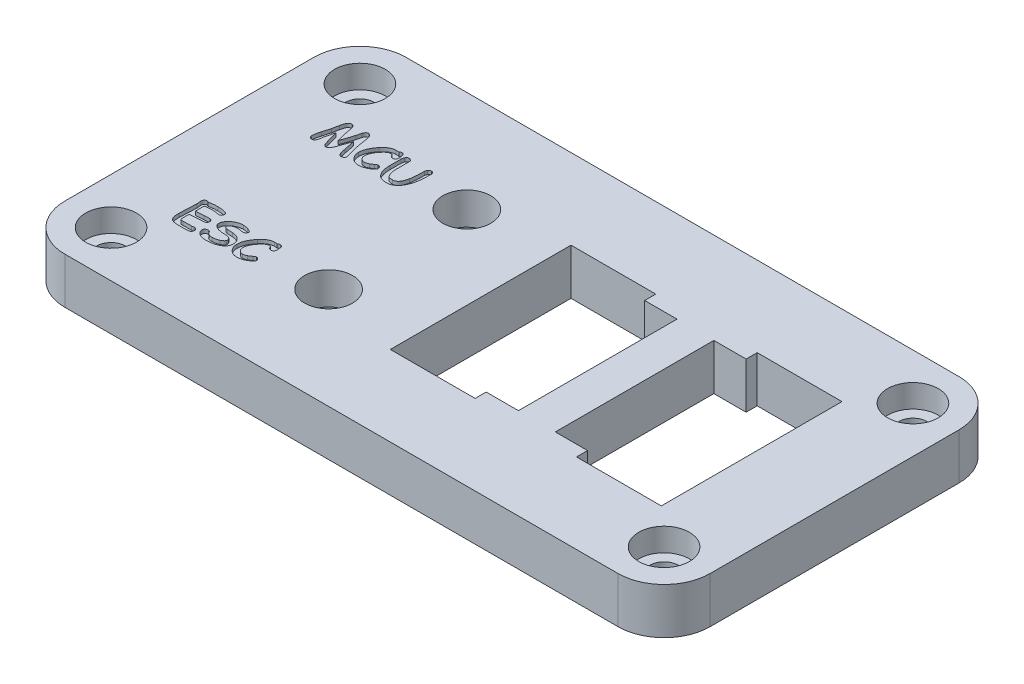
SolidWorks part; units mm, degrees
ref_plane "Front Plane" through (0, 0, 0) normal (0, 0, 1) x (1, 0, 0)
ref_plane "Top Plane" through (0, 0, 0) normal (0, 1, 0) x (1, 0, 0)
ref_plane "Right Plane" through (0, 0, 0) normal (1, 0, 0) x (0, 0, -1)
sketch "Sketch1" plane through (0, 0, 0) normal (0, 1, 0) x (1, 0, 0)
  line L0 (-1000, 0) -> (49000, 0) construction
  line L1 (-35, -18.5) -> (35, -18.5)
  line L2 (-35, -18.5) -> (-35, 18.5)
  line L3 (-35, 18.5) -> (35, 18.5)
  line L4 (35, -18.5) -> (35, 18.5)
  line L5 (-35, -18.5) -> (35, 18.5) construction
  line L6 (-35, 18.5) -> (35, -18.5) construction
  line L7 (-1002.5399, 13.5) -> (48997.4601, 13.5) construction
  line L8 (-1000.0562, -13.5) -> (48999.9438, -13.5) construction
  line L9 (-12.4, -1000) -> (-12.4, 49000) construction
  line L10 (26, -8.6) -> (13.3, -8.6)
  line L11 (26, -8.6) -> (26, 8.6)
  line L12 (26, 8.6) -> (13.3, 8.6)
  line L13 (13.3, -8.6) -> (13.3, 8.6)
  line L14 (26, -8.6) -> (13.3, 8.6) construction
  line L15 (26, 8.6) -> (13.3, -8.6) construction
  line L16 (26, 8.6) -> (16.8, 8.6)
  line L17 (26, 8.6) -> (26, 9.8)
  line L18 (26, 9.8) -> (16.8, 9.8)
  line L19 (16.8, 8.6) -> (16.8, 9.8)
  line L20 (26, -8.6) -> (16.8, -8.6)
  line L21 (26, -8.6) -> (26, -9.8)
  line L22 (26, -9.8) -> (16.8, -9.8)
  line L23 (16.8, -8.6) -> (16.8, -9.8)
  line L24 (-3.4, -8.6) -> (9.3, -8.6)
  line L25 (-3.4, -8.6) -> (-3.4, 8.6)
  line L26 (-3.4, 8.6) -> (9.3, 8.6)
  line L27 (9.3, -8.6) -> (9.3, 8.6)
  line L28 (-3.4, -8.6) -> (9.3, 8.6) construction
  line L29 (-3.4, 8.6) -> (9.3, -8.6) construction
  line L38 (-30, -986.4854) -> (-30, 49013.5146) construction
  line L39 (30, -986.4123) -> (30, 49013.5877) construction
  line L41 (-3.4, 8.6) -> (5.8, 8.6)
  line L42 (-3.4, 8.6) -> (-3.4, 9.8)
  line L43 (-3.4, 9.8) -> (5.8, 9.8)
  line L44 (5.8, 8.6) -> (5.8, 9.8)
  line L45 (-3.4, -8.6) -> (5.8, -8.6)
  line L46 (-3.4, -8.6) -> (-3.4, -9.8)
  line L47 (-3.4, -9.8) -> (5.8, -9.8)
  line L48 (5.8, -8.6) -> (5.8, -9.8)
  circle A0 centre (-12.4, 7.5) radius 2.6
  circle A1 centre (-12.4, -7.5) radius 2.6
  circle A2 centre (30, 13.5) radius 1.55
  circle A3 centre (30, -13.5) radius 1.55
  circle A4 centre (-30, -13.5) radius 1.55
  circle A5 centre (-30, 13.5) radius 1.55
  point P0 (0, 0)
  point P11 (19.65, 0)
  point P23 (2.95, 0)
  dimension "D20" = 5.2
  dimension "D21" = 5.2
  dimension "D26" = 3.1
  dimension "D28" = 3.1
  dimension "D30" = 3.1
  dimension "D32" = 3.1
  dimension "D1" = 37
  dimension "D2" = 70
  dimension "D3" = 5
  dimension "D4" = 5
  dimension "D5" = 17.2
  dimension "D6" = 12.7
  dimension "D7" = 9
  dimension "D8" = 1.2
  dimension "D9" = 1.2
  dimension "D10" = 9.2
  dimension "D11" = 9.2
  dimension "D12" = 12.7
  dimension "D13" = 17.2
  dimension "D14" = 4
  dimension "D15" = 1.2
  dimension "D16" = 1.2
  dimension "D17" = 9.2
  dimension "D18" = 9.2
  dimension "D19" = 9
  dimension "D22" = 7.5
  dimension "D23" = 7.5
  dimension "D24" = 5
  dimension "D25" = 5
  dimension "D27" = 0
  dimension "D29" = 0
  dimension "D31" = 0
  dimension "D33" = 0
extrude "Boss-Extrude1" add sketch "Sketch1" along normal blind 5 contours L1 L4 L3 L2 A5 A4 A3 A2 A1 A0 L23 L10 L13 L12 L19 L18 L17 L11 L21 L22 L24 L48 L47 L46 L25 L42 L43 L44 L26 L27
sketch "Sketch2" plane through (0, 5, 0) normal (0, 1, 0) x (1, 0, 0)
  circle A0 centre (-30, 13.5) radius 2.75
  circle A1 centre (30, 13.5) radius 2.75
  circle A2 centre (30, -13.5) radius 2.75
  circle A3 centre (-30, -13.5) radius 2.75
  dimension "D1" = 5.5
  dimension "D2" = 5.5
  dimension "D3" = 5.5
  dimension "D4" = 5.5
extrude "Cut-Extrude1" cut sketch "Sketch2" against normal blind 2.5
sketch "Sketch3" plane through (0, 0, 0) normal (0, -1, 0) x (1, 0, 0)
  circle A0 centre (-12.4, 7.5) radius 3.05
  circle A1 centre (-12.4, -7.5) radius 3.05
  dimension "D1" = 6.1
  dimension "D2" = 6.1
extrude "Cut-Extrude2" cut sketch "Sketch3" against normal blind 1.5
sketch "Sketch4" plane through (0, 5, 0) normal (0, 1, 0) x (1, 0, 0)
  line L0 (-1012.9, 7.5) -> (48987.1, 7.5) construction
  line L1 (-1012.9, -7.5) -> (48987.1, -7.5) construction
  text T0 "MCU" font "Comic Sans MS" height 3.5
  text T1 "ESC" font "Comic Sans MS" height 3.5
  point P8 (-26.2261, -10.2749)
  point P9 (0, 0)
  point P10 (0, 0)
  point P11 (-27.8787, -9.7001)
  point P12 (-27.8787, -8.766)
  point P13 (-27.8787, -9.4127)
  point P14 (0, 0)
  point P15 (0, 0)
extrude "Cut-Extrude3" cut sketch "Sketch4" against normal blind 0.4
fillet "Fillet1" radius 5 4 edges at (-35, 2.5, -18.5) (35, 2.5, -18.5) (35, 2.5, 18.5) (-35, 2.5, 18.5)
